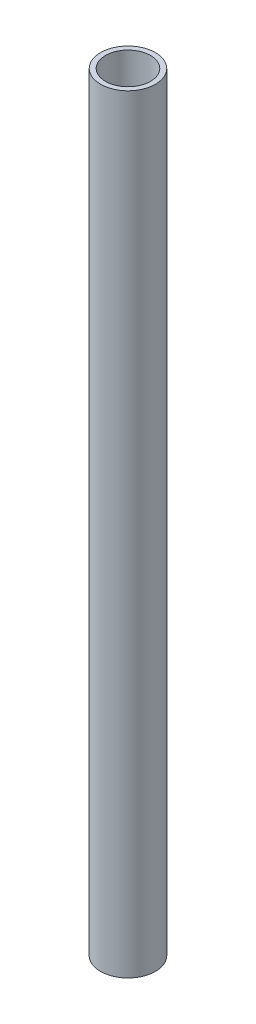
SolidWorks part; units mm, degrees
ref_plane "Front Plane" through (0, 0, 0) normal (0, 0, 1) x (1, 0, 0)
ref_plane "Top Plane" through (0, 0, 0) normal (0, 1, 0) x (1, 0, 0)
ref_plane "Right Plane" through (0, 0, 0) normal (1, 0, 0) x (0, 0, -1)
sketch "Sketch1" plane through (0, 0, 0) normal (0, 1, 0) x (1, 0, 0)
  circle A0 centre (0, 0) radius 12.7
  circle A1 centre (0, 0) radius 10.414
  dimension "D1" = 25.4
  dimension "D2" = 20.828
extrude "Boss-Extrude1" add sketch "Sketch1" along normal blind 355.6
